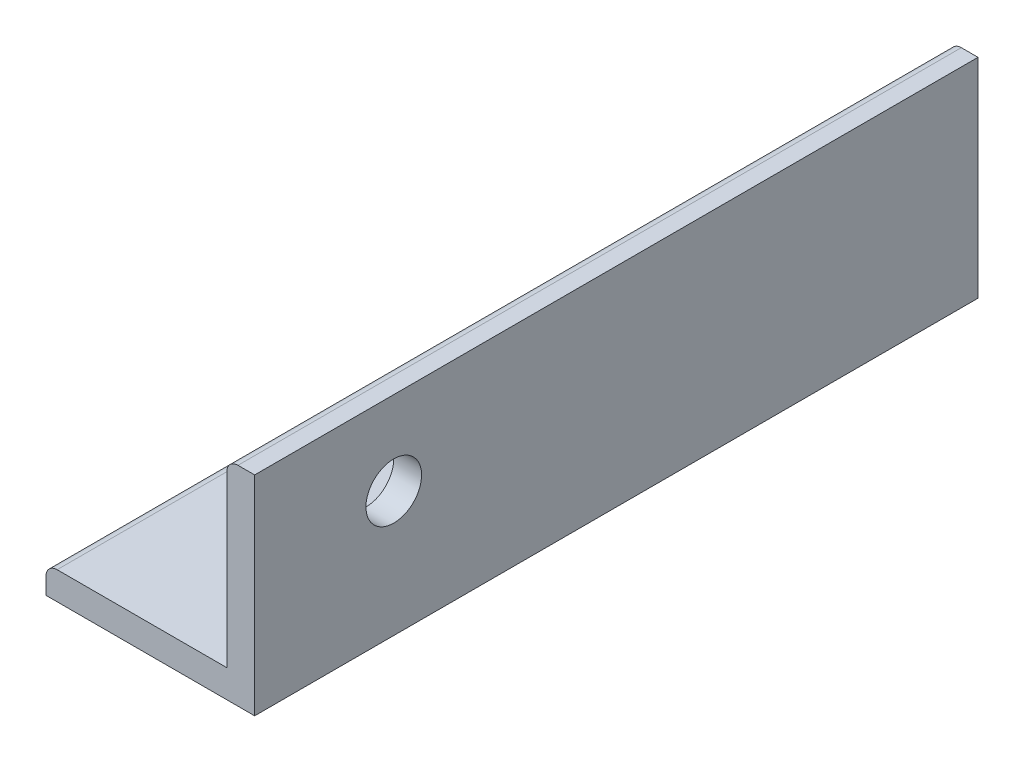
SolidWorks part; units mm, degrees
ref_plane "前视基准面" through (0, 0, 0) normal (0, 0, 1) x (1, 0, 0)
ref_plane "上视基准面" through (0, 0, 0) normal (0, 1, 0) x (1, 0, 0)
ref_plane "右视基准面" through (0, 0, 0) normal (1, 0, 0) x (0, 0, -1)
sketch "草图1" plane through (0, 0, 0) normal (0, 0, 1) x (1, 0, 0)
  line L0 (0, 0) -> (0, 15)
  line L1 (0, 15) -> (-2, 15)
  line L2 (-2, 15) -> (-2, 2)
  line L3 (0, 0) -> (-15, 0)
  line L4 (-15, 0) -> (-15, 2)
  line L5 (-15, 2) -> (-2, 2)
  dimension "D1" = 15
  dimension "D2" = 15
  dimension "D3" = 2
  dimension "D4" = 2
extrude "凸台-拉伸1" add sketch "草图1" along normal blind 52
fillet "圆角1" radius 0.8 2 edges at (-15, 2, 26) (-2, 15, 26)
sketch "草图2" plane through (0, 2, 0) normal (0, 1, 0) x (1, 0, 0)
  line L2 (-2, -52) -> (-2, 0) construction
  line L4 (-2, 0) -> (-14.2, 0) construction
  circle A1 centre (-8, -10) radius 2
  dimension "D1" = 4
  dimension "D2" = 10
  dimension "D6" = 6
sketch "草图3" plane through (-2, 0, 0) normal (-1, 0, 0) x (0, 0, 1)
  line L0 (52, 14.2) -> (52, 2) construction
  line L2 (52, 2) -> (0, 2) construction
  circle A0 centre (42, 9) radius 2
  dimension "D1" = 4
  dimension "D2" = 10
  dimension "D3" = 7
extrude "切除-拉伸2" cut sketch "草图3" against normal blind 2
